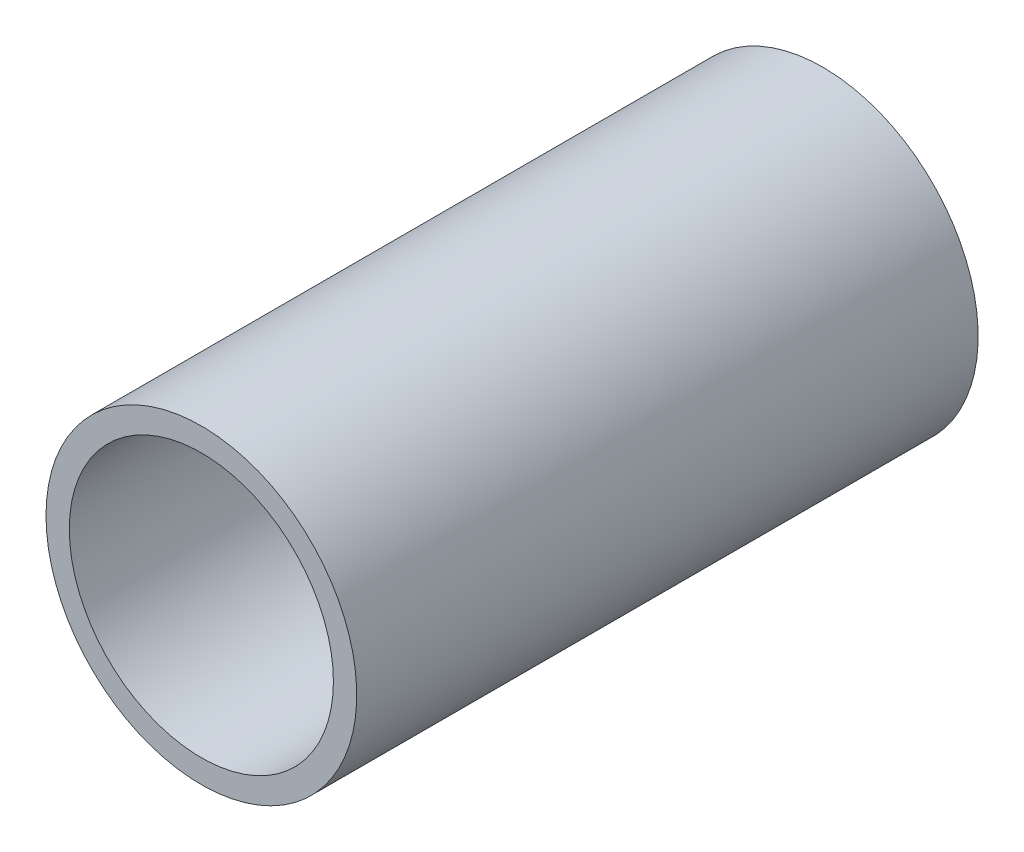
SolidWorks part; units mm, degrees
ref_plane "Plan de face" through (0, 0, 0) normal (0, 0, 1) x (1, 0, 0)
ref_plane "Plan de dessus" through (0, 0, 0) normal (0, 1, 0) x (1, 0, 0)
ref_plane "Plan de droite" through (0, 0, 0) normal (1, 0, 0) x (0, 0, -1)
sketch "Esquisse1" plane through (0, 0, -4) normal (0, 0, -1) x (-1, 0, 0)
  circle A1 centre (43.5381, 71.053) radius 10
  arc A2 (32.9551, 68.053) -> (32.9551, 74.053) centre (43.5381, 71.053) ccw construction
  circle A5 centre (43.5381, 71.053) radius 8.5
  dimension "D1" = 17
  dimension "D2" = 1.5
extrude "Boss.-Extru.1" add sketch "Esquisse1" along normal blind 40
